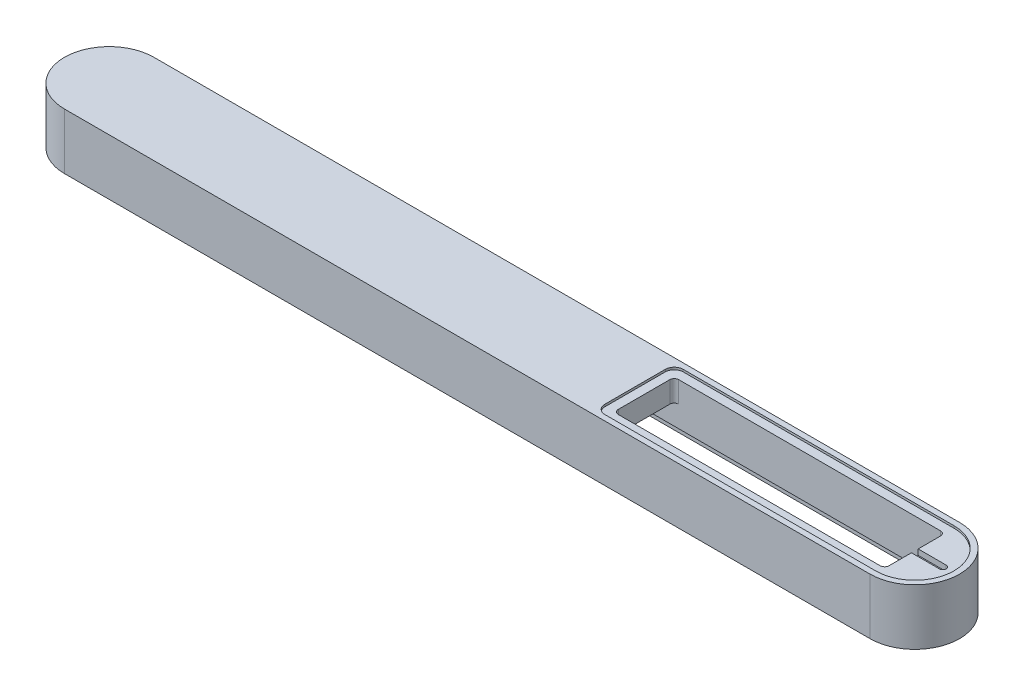
SolidWorks part; units mm, degrees
material "Teak"
ref_plane "Front Plane" through (0, 0, 0) normal (0, 0, 1) x (1, 0, 0)
ref_plane "Top Plane" through (0, 0, 0) normal (0, 1, 0) x (1, 0, 0)
ref_plane "Right Plane" through (0, 0, 0) normal (1, 0, 0) x (0, 0, -1)
sketch "Sketch1" plane through (0, 0, 0) normal (0, 1, 0) x (1, 0, 0)
  line L1 (-360, 40) -> (360, 40)
  line L3 (-360, -40) -> (360, -40)
  arc A0 (360, 40) -> (360, -40) centre (360, 0) cw
  arc A1 (-360, -40) -> (-360, 40) centre (-360, 0) cw
  point P0 (0, 0)
  dimension "D4" = 40
  dimension "D3" = 40
  dimension "D1" = 360
  dimension "D2" = 40
  dimension "D5" = 80
  dimension "D6" = 360
  dimension "D7" = 360
  dimension "D8" = 360
extrude "Boss-Extrude1" add sketch "Sketch1" along normal blind 50
sketch "Sketch4" plane through (0, 0, 0) normal (0, -1, 0) x (1, 0, 0)
  line L8 (360, 35) -> (-360, 35)
  line L9 (-360, -35) -> (360, -35)
  line L10 (360, 35) -> (-360, 35)
  line L11 (-360, -35) -> (360, -35)
  arc A6 (-360, 35) -> (-360, -35) centre (-360, 0) ccw
  arc A7 (360, -35) -> (360, 35) centre (360, 0) ccw
  arc A8 (-360, 35) -> (-360, -35) centre (-360, 0) ccw
  arc A9 (360, -35) -> (360, 35) centre (360, 0) ccw
  dimension "D1" = 5
extrude "Cut-Extrude2" cut sketch "Sketch4" against normal blind 4
sketch "Sketch6" plane through (0, 50, 0) normal (0, 1, 0) x (1, 0, 0)
  line L3 (360, 35) -> (-360, 35)
  line L4 (360, 35) -> (118, 35)
  line L5 (110, 27) -> (110, -27)
  line L6 (-360, -35) -> (360, -35)
  line L7 (118, -35) -> (360, -35)
  arc A1 (110, 27) -> (118, 35) centre (118, 27) cw
  arc A2 (360, -35) -> (360, 35) centre (360, 0) ccw
  arc A3 (360, -35) -> (360, 35) centre (360, 0) ccw
  arc A4 (118, -35) -> (110, -27) centre (118, -27) cw
  dimension "D4" = 8
  dimension "D7" = 8
  dimension "D3" = 250
  dimension "D5" = 8
  dimension "D6" = 8
  dimension "D8" = 8
  dimension "D9" = 8
  dimension "D1" = 5
  dimension "D2" = 5
extrude "Cut-Extrude5" cut sketch "Sketch6" against normal blind 2
sketch "Sketch2" plane through (0, 4, 0) normal (0, -1, 0) x (1, 0, 0)
  line L0 (360, -40) -> (-360, -40) construction
  line L1 (356, -27) -> (-356, -27)
  line L2 (360, -23) -> (360, 23)
  line L3 (356, 27) -> (-356, 27)
  line L4 (-360, -23) -> (-360, 23)
  line L5 (-360, 40) -> (360, 40) construction
  arc A0 (356, -27) -> (360, -23) centre (356, -23) ccw
  arc A1 (360, 23) -> (356, 27) centre (356, 23) ccw
  arc A2 (-360, -23) -> (-356, -27) centre (-356, -23) ccw
  arc A3 (-356, 27) -> (-360, 23) centre (-356, 23) ccw
  point P1 (0, 0)
  dimension "D3" = 4
  dimension "D4" = 720
  dimension "D1" = 8
  dimension "D7" = 4
  dimension "D9" = 8
  dimension "D11" = 8
  dimension "D12" = 4
  dimension "D14" = 4
  dimension "D15" = 4
  dimension "D16" = 8
  dimension "D5" = 13
  dimension "D6" = 13
  dimension "D8" = 4
  dimension "D13" = 4
  dimension "D17" = 360
sketch "Sketch7" plane through (0, 48, 0) normal (0, 1, 0) x (1, 0, 0)
  line L1 (122, 27) -> (356, 27)
  line L2 (118, 23) -> (118, -23)
  line L3 (122, -27) -> (356, -27)
  line L4 (360, 23) -> (360, -23)
  line L5 (110, 27) -> (110, -27) construction
  line L6 (118, -35) -> (360, -35) construction
  line L7 (360, 35) -> (118, 35) construction
  arc A0 (122, 27) -> (118, 23) centre (122, 23) ccw
  arc A1 (118, -23) -> (122, -27) centre (122, -23) ccw
  arc A2 (360, 23) -> (356, 27) centre (356, 23) ccw
  arc A3 (356, -27) -> (360, -23) centre (356, -23) ccw
  dimension "D5" = 8
  dimension "D9" = 8
  dimension "D12" = 8
  dimension "D15" = 8
  dimension "D1" = 8
  dimension "D2" = 8
  dimension "D3" = 8
  dimension "D4" = 4
  dimension "D6" = 4
  dimension "D7" = 4
  dimension "D8" = 4
  dimension "D10" = 4
  dimension "D11" = 4
  dimension "D13" = 4
  dimension "D14" = 4
extrude "Cut-Extrude7" cut sketch "Sketch7" against normal blind 20
extrude "Cut-Extrude9" cut sketch "Sketch2" against normal blind 25 contours L3 A3 L4 A2 L1 A0 L2 A1
sketch "Sketch15" plane through (0, 4, 0) normal (0, -1, 0) x (1, 0, 0)
  line L1 (360, -30) -> (-360, -30)
  line L2 (360, -22) -> (360, 22)
  line L3 (360, 30) -> (-360, 30)
  line L4 (-360, -22) -> (-360, 22)
  line L6 (-360, 40) -> (360, 40) construction
  arc A0 (360, -30) -> (360, -22) centre (360, -26) ccw
  arc A1 (360, 22) -> (360, 30) centre (360, 26) ccw
  arc A2 (360, 22) -> (360, 30) centre (360, 26) ccw
  arc A3 (-360, -30) -> (-360, -22) centre (-360, -26) cw
  arc A4 (-360, 30) -> (-360, 22) centre (-360, 26) ccw
  point P0 (0, 0)
  point P8 (0, 0)
  arc M1 (-360, 23) -> (-356, 27) centre (-356, 23) cw
  line M2 (-356, 27) -> (356, 27)
  arc M3 (356, 27) -> (360, 23) centre (356, 23) cw
  line M4 (360, 23) -> (360, -23)
  arc M5 (360, -23) -> (356, -27) centre (356, -23) cw
  line M6 (356, -27) -> (-356, -27)
  arc M7 (-356, -27) -> (-360, -23) centre (-356, -23) cw
  line M8 (-360, -23) -> (-360, 23)
  dimension "D3" = 4
  dimension "D4" = 4
  dimension "D6" = 4
  dimension "D9" = 4
  dimension "D2" = 60
  dimension "D5" = 360
  dimension "D7" = 4
  dimension "D8" = 360
  dimension "D11" = 360
  dimension "D13" = 10
  dimension "D14" = 360
extrude "Cut-Extrude14" cut sketch "Sketch15" against normal blind 6 contours A3 L1 A0 M4 M5 M6 M7 M8 | L3 A4 A1 M8 M1 M2 M3 M4
hole_wizard "Hole1" positions "Sketch17" profile "Sketch16" legacy end condition through all
sketch "Sketch17" plane through (0, 4, 0) normal (0, -1, 0) x (-1, 0, 0)
  line L1 (360, -40) -> (-360, -40) construction
  line L2 (-360, 22) -> (-360, -22) construction
  point P0 (-385, 0)
  dimension "D1" = 25
  dimension "D2" = 40
sketch "Sketch16" plane through (385, 4, 0) normal (1, 0, 0) x (0, 0, -1)
  line L0 (0, 0) -> (0, 46)
  line L1 (0, 46) -> (3, 46)
  line L2 (3, 46) -> (3, 0)
  line L5 (3, 0) -> (0, 0)
  line L11 (0, -6.35) -> (0, 107.95) construction
  dimension "Thru Hole Dia." = 6
  dimension "Thru Hole Depth" = 46
sketch "Sketch18" plane through (0, 48, 0) normal (0, 1, 0) x (1, 0, 0)
  line L0 (360, -23) -> (360, 23) construction
  line L1 (385, -3) -> (360, -3)
  line L2 (385, -3) -> (385, 3)
  line L3 (385, 3) -> (360, 3)
  line L4 (360, -3) -> (360, 3)
  circle A0 centre (385, 0) radius 3 construction
  dimension "D1" = 25
extrude "Cut-Extrude15" cut sketch "Sketch18" against normal blind 5
